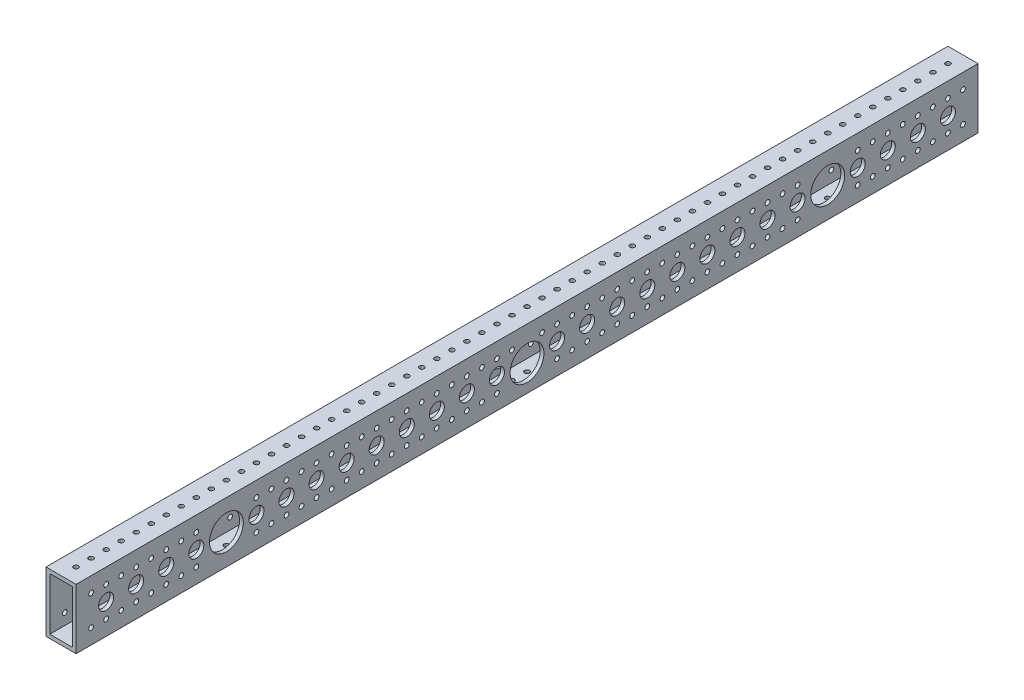
SolidWorks part; units mm, degrees
material "6061 Alloy"
ref_plane "Front Plane" through (0, 0, 0) normal (0, 0, 1) x (1, 0, 0)
ref_plane "Top Plane" through (0, 0, 0) normal (0, 1, 0) x (1, 0, 0)
ref_plane "Right Plane" through (0, 0, 0) normal (1, 0, 0) x (0, 0, -1)
sketch "Sketch1" plane through (0, 0, 0) normal (0, 0, 1) x (1, 0, 0)
  line L1 (12.7, 25.4) -> (-12.7, 25.4)
  line L2 (12.7, 25.4) -> (12.7, -25.4)
  line L3 (12.7, -25.4) -> (-12.7, -25.4)
  line L4 (-12.7, 25.4) -> (-12.7, -25.4)
  line L5 (12.7, 25.4) -> (-12.7, -25.4) construction
  line L6 (12.7, -25.4) -> (-12.7, 25.4) construction
  point P0 (0, 0)
  dimension "D1" = 25.4
  dimension "D2" = 50.8
extrude "Boss-Extrude1" add sketch "Sketch1" along normal blind 762
shell "Shell1" thickness 3.175
hole_wizard "#21 (0.159) Diameter Hole1" positions "Sketch2" profile "Sketch3" hole size "#21" standard "ANSI Inch" end condition through all
sketch "Sketch2" plane through (0, 25.4, 0) normal (0, 1, 0) x (1, 0, 0)
  line L0 (12.7, 0) -> (-12.7, 0) construction
  line L1 (12.7, -762) -> (12.7, 0) construction
  point P0 (0, -12.7)
  dimension "D1" = 12.7
  dimension "D2" = 12.7
sketch "Sketch3" plane through (0, 25.4, 12.7) normal (1, 0, 0) x (0, 0, 1)
  line L0 (0, 0) -> (0, 50.8)
  line L1 (0, 50.8) -> (2.0193, 50.8)
  line L2 (2.0193, 50.8) -> (2.0193, 0)
  line L5 (2.0193, 0) -> (0, 0)
  line L11 (0, -6.35) -> (0, 107.95) construction
  dimension "Thru Hole Dia." = 4.0386
  dimension "Thru Hole Depth" = 50.8
pattern_linear "LPattern1" count 59 spacing 12.7 along (0, 0, 1) of "#21 (0.159) Diameter Hole1"
hole_wizard "#21 (0.159) Diameter Hole2" positions "Sketch4" profile "Sketch5" hole size "#21" standard "ANSI Inch" end condition through all
sketch "Sketch4" plane through (-12.7, 0, 0) normal (-1, 0, 0) x (0, 0, 1)
  line L0 (762, 25.4) -> (0, 25.4) construction
  line L1 (0, 25.4) -> (0, -25.4) construction
  point P0 (12.7, 12.7)
  dimension "D1" = 12.7
  dimension "D2" = 12.7
sketch "Sketch5" plane through (-12.7, 12.7, 12.7) normal (0, 1, 0) x (0, 0, 1)
  line L0 (0, 0) -> (0, 25.4)
  line L1 (0, 25.4) -> (2.0193, 25.4)
  line L2 (2.0193, 25.4) -> (2.0193, 0)
  line L5 (2.0193, 0) -> (0, 0)
  line L11 (0, -6.35) -> (0, 107.95) construction
  dimension "Thru Hole Dia." = 4.0386
  dimension "Thru Hole Depth" = 25.4
pattern_linear "LPattern2" count 59 spacing 12.7 along (0, 0, 1) count 2 spacing 25.4 along (0, -1, 0) skipping (8, 0), (8, 1), (9, 0), (9, 1), (10, 0), (10, 1), (28, 1), (29, 0), (29, 1), (30, 1), (48, 0), (48, 1), (49, 0), (49, 1), (50, 0), (50, 1) of "#21 (0.159) Diameter Hole2"
hole_wizard "1/2 (0.5) Diameter Hole1" positions "Sketch6" profile "Sketch7" hole size "1/2" standard "ANSI Inch" end condition through all
sketch "Sketch6" plane through (-12.7, 0, 0) normal (-1, 0, 0) x (0, 0, 1)
  line L0 (762, 25.4) -> (0, 25.4) construction
  line L1 (0, 25.4) -> (0, -25.4) construction
  point P0 (25.4, 0)
  dimension "D1" = 25.4
  dimension "D2" = 25.4
sketch "Sketch7" plane through (-12.7, 0, 25.4) normal (0, 1, 0) x (0, 0, 1)
  line L0 (0, 0) -> (0, 25.4)
  line L1 (0, 25.4) -> (6.35, 25.4)
  line L2 (6.35, 25.4) -> (6.35, 0)
  line L5 (6.35, 0) -> (0, 0)
  line L11 (0, -6.35) -> (0, 107.95) construction
  dimension "Thru Hole Dia." = 12.7
  dimension "Thru Hole Depth" = 25.4
pattern_linear "LPattern3" count 29 spacing 25.4 along (0, 0, 1) skipping (4, 0), (14, 0), (24, 0) of "1/2 (0.5) Diameter Hole1"
sketch "Sketch8" plane through (-12.7, 0, 0) normal (-1, 0, 0) x (0, 0, 1)
  line L0 (0, 25.4) -> (0, -25.4) construction
  line L1 (762, -25.4) -> (0, -25.4) construction
  line L2 (762, 25.4) -> (0, 25.4) construction
  line L4 (762, 25.4) -> (762, -25.4) construction
  point P0 (381, -3.175)
  point P5 (635, 0)
  point P6 (127, 0)
  dimension "D1" = 381
  dimension "D2" = 22.225
  dimension "D3" = 25.4
  dimension "D5" = 127
  dimension "D4" = 127
hole_wizard "#97 (1.125) Diameter Hole2" positions "Sketch13" profile "Sketch14" hole size "#97" standard "ANSI Inch" end condition through all
sketch "Sketch13" plane through (-12.7, 0, 0) normal (-1, 0, 0) x (0, 0, 1)
  point P0 (127, 0)
  point P3 (635, 0)
  point P6 (381, -3.175)
sketch "Sketch14" plane through (-12.7, 0, 127) normal (0, 1, 0) x (0, 0, 1)
  line L0 (0, 0) -> (0, 25.4)
  line L1 (0, 25.4) -> (14.2875, 25.4)
  line L2 (14.2875, 25.4) -> (14.2875, 0)
  line L5 (14.2875, 0) -> (0, 0)
  line L11 (0, -6.35) -> (0, 107.95) construction
  dimension "Thru Hole Dia." = 28.575
  dimension "Thru Hole Depth" = 25.4
equation "\"Length\"= 30"
equation "\"D1@Boss-Extrude1\"= \"Length\""
equation "\"D1@Sketch8\"=\"Length\"/2"
equation "\"Wheel Distance\"= 5"
equation "\"D5@Sketch8\"=\"Wheel Distance\""
equation "\"D4@Sketch8\"=\"Wheel Distance\""
